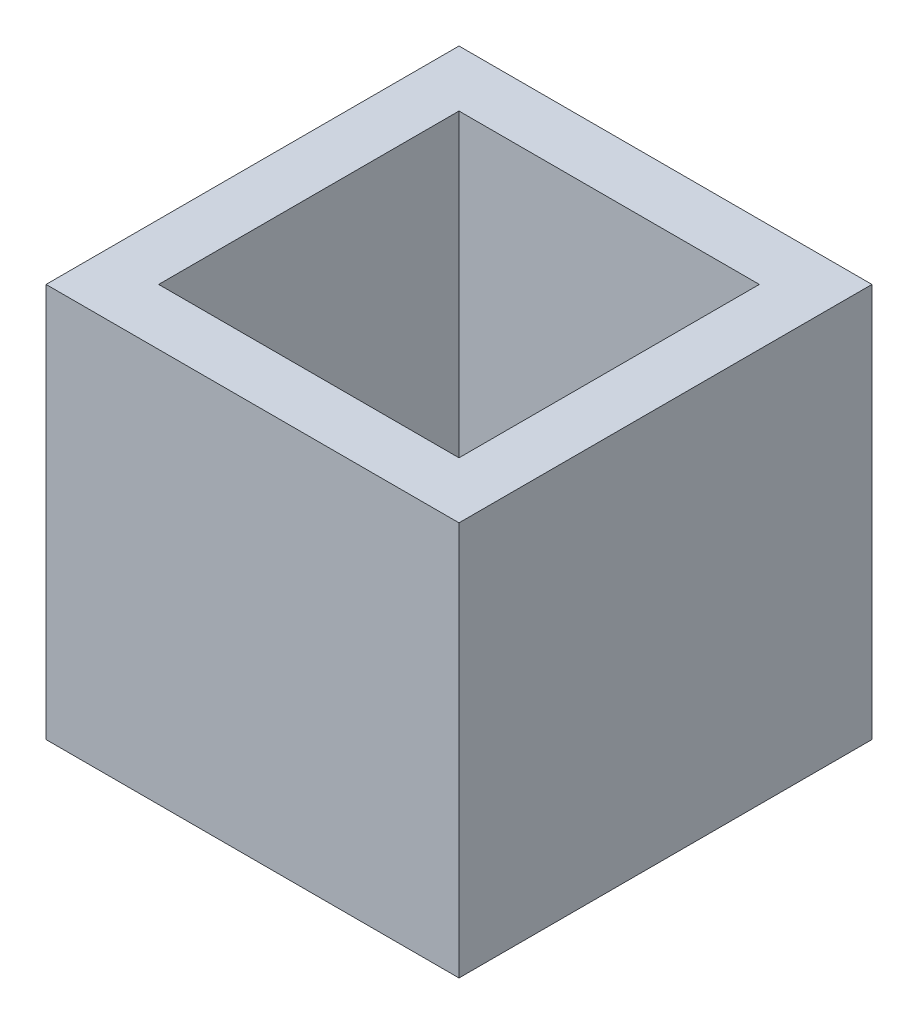
SolidWorks part; units mm, degrees
ref_plane "Front Plane" through (0, 0, 0) normal (0, 0, 1) x (1, 0, 0)
ref_plane "Top Plane" through (0, 0, 0) normal (0, 1, 0) x (1, 0, 0)
ref_plane "Right Plane" through (0, 0, 0) normal (1, 0, 0) x (0, 0, -1)
sketch "Sketch1" plane through (0, 0, 0) normal (0, 1, 0) x (1, 0, 0)
  line L1 (0, 0) -> (12, 0)
  line L2 (0, 0) -> (0, 12)
  line L3 (0, 12) -> (12, 12)
  line L4 (12, 0) -> (12, 12)
  dimension "D1" = 12
  dimension "D2" = 12
extrude "Boss-Extrude1" add sketch "Sketch1" along normal blind 11
shell "Shell1" thickness 2
sketch "Sketch2" plane through (0, 2, 0) normal (0, 1, 0) x (1, 0, 0)
  line L0 (12, 0) -> (12, 12) construction
  line L1 (12, 12) -> (0, 12) construction
  circle A0 centre (6, 6) radius 3
  point P0 (6, 6)
  dimension "D3" = 6
  dimension "D1" = 6
  dimension "D2" = 6
sketch "Sketch3" plane through (0, 0, 0) normal (0, -1, 0) x (1, 0, 0)
  circle A0 centre (6, -4.73) radius 0.625
  circle A1 centre (6, -7.27) radius 0.625
  point P0 (6, -4.73)
  point P1 (6, -7.27)
  dimension "D1" = 1.25
  dimension "D2" = 1.25
extrude "Cut-Extrude1" cut sketch "Sketch3" against normal blind 10
sketch "Sketch4" plane through (0, 11, 0) normal (0, 1, 0) x (1, 0, 0)
  line L13 (12, 0) -> (12, 12) construction
  line L14 (0, 0) -> (12, 0) construction
  line L15 (0, 12) -> (0, 0) construction
  line L16 (12, 12) -> (0, 12) construction
  line L17 (11.5, 0.5) -> (11.5, 11.5)
  line L18 (0.5, 0.5) -> (11.5, 0.5)
  line L19 (0.5, 11.5) -> (0.5, 0.5)
  line L20 (11.5, 11.5) -> (0.5, 11.5)
  line L21 (11.5, 0.5) -> (11.5, 11.5)
  line L22 (0.5, 0.5) -> (11.5, 0.5)
  line L23 (0.5, 11.5) -> (0.5, 0.5)
  line L24 (11.5, 11.5) -> (0.5, 11.5)
  line L25 (12, 0) -> (12, 12)
  line L26 (0, 0) -> (12, 0)
  line L27 (0, 12) -> (0, 0)
  line L28 (12, 12) -> (0, 12)
  dimension "D1" = 0.5
extrude "Cut-Extrude2" cut sketch "Sketch4" against normal through all
sketch "Sketch5" plane through (0, 0, 0) normal (0, -1, 0) x (1, 0, 0)
  line L4 (11.5, -11.5) -> (11.5, -0.5)
  line L5 (11.5, -0.5) -> (0.5, -0.5)
  line L6 (0.5, -0.5) -> (0.5, -11.5)
  line L7 (0.5, -11.5) -> (11.5, -11.5)
  line L8 (11.5, -11.5) -> (11.5, -0.5)
  line L9 (11.5, -0.5) -> (0.5, -0.5)
  line L10 (0.5, -0.5) -> (0.5, -11.5)
  line L11 (0.5, -11.5) -> (11.5, -11.5)
  dimension "D1" = 0
extrude "Cut-Extrude3" cut sketch "Sketch5" against normal blind 0.5
